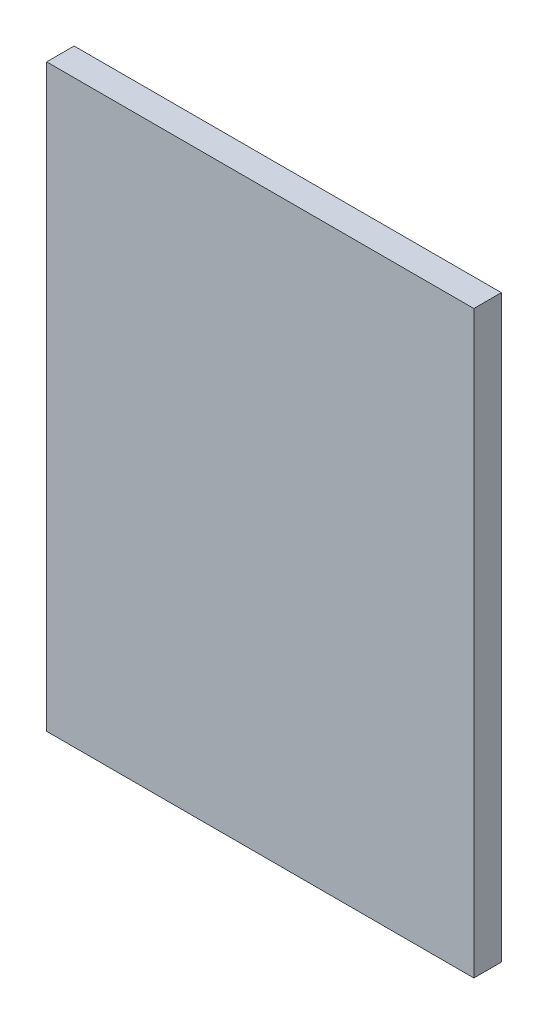
SolidWorks part; units mm, degrees
material "Balsa"
ref_plane "Front Plane" through (0, 0, 0) normal (0, 0, 1) x (1, 0, 0)
ref_plane "Top Plane" through (0, 0, 0) normal (0, 1, 0) x (1, 0, 0)
ref_plane "Right Plane" through (0, 0, 0) normal (1, 0, 0) x (0, 0, -1)
sketch "Sketch1" plane through (0, 0, 0) normal (0, 0, 1) x (1, 0, 0)
  line L1 (-140, 190) -> (140, 190)
  line L2 (-140, 190) -> (-140, -190)
  line L3 (-140, -190) -> (140, -190)
  line L4 (140, 190) -> (140, -190)
  line L5 (-140, 190) -> (140, -190) construction
  line L6 (-140, -190) -> (140, 190) construction
  point P0 (0, 0)
  dimension "D1" = 280
  dimension "D2" = 380
extrude "Boss-Extrude1" add sketch "Sketch1" along normal blind 18
